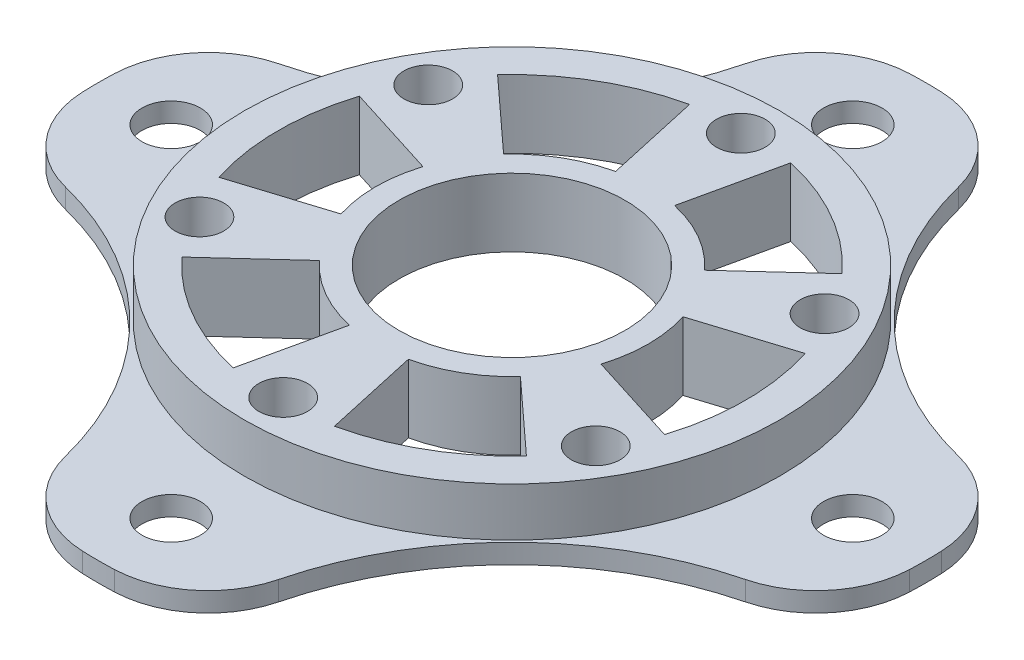
SolidWorks part; units mm, degrees
ref_plane "Front Plane" through (0, 0, 0) normal (0, 0, 1) x (1, 0, 0)
ref_plane "Top Plane" through (0, 0, 0) normal (0, 1, 0) x (1, 0, 0)
ref_plane "Right Plane" through (0, 0, 0) normal (1, 0, 0) x (0, 0, -1)
sketch "Sketch1" plane through (0, 0, 0) normal (0, 1, 0) x (1, 0, 0)
  circle A0 centre (0, 0) radius 27.5
  dimension "D1" = 55
extrude "Boss-Extrude1" add sketch "Sketch1" against normal blind 5
sketch "Sketch2" plane through (0, -5, 0) normal (0, -1, 0) x (1, 0, 0)
  circle A0 centre (0, 0) radius 42.5
  dimension "D1" = 85
extrude "Boss-Extrude2" add sketch "Sketch2" along normal blind 2
sketch "Sketch3" plane through (0, -5, 0) normal (0, 1, 0) x (1, 0, 0)
  circle A0 centre (0, 35) radius 3
  circle A1 centre (35, 0) radius 3
  circle A2 centre (0, -35) radius 3
  circle A3 centre (-35, 0) radius 3
  circle A4 centre (0, 0) radius 42.5 construction
  arc A5 (-10, 41.3068) -> (-41.3068, 10) centre (-42.9586, 42.9586) cw
  arc A6 (41.3068, 10) -> (10, 41.3068) centre (42.9586, 42.9586) cw
  arc A7 (10, -41.3068) -> (41.3068, -10) centre (42.9586, -42.9586) cw
  arc A8 (-41.3068, -10) -> (-10, -41.3068) centre (-42.9586, -42.9586) cw
  circle A10 centre (0, 0) radius 42.5
  circle A11 centre (0, 0) radius 42.5
  point P12 (0, 0)
  point P27 (0, 0)
  circle M3 centre (0, 0) radius 42.5
  dimension "D1" = 6
  dimension "D6" = 33
  dimension "D2" = 35
  dimension "D3" = 4
  dimension "D4" = 10
  dimension "D5" = 10
  dimension "D8" = 0
  dimension "D7" = 4
extrude "Cut-Extrude1" cut sketch "Sketch3" against normal blind 2 contours A5 M3 | A0 | A6 M3 | A1 | A2 | A7 M3 | A8 M3 | A3
sketch "Sketch4" plane through (0, 0, 0) normal (0, 1, 0) x (1, 0, 0)
  circle A0 centre (0, 0) radius 11.6
  circle A1 centre (0, 23.5) radius 2.5
  circle A2 centre (20.3516, 11.75) radius 2.5
  circle A3 centre (20.3516, -11.75) radius 2.5
  circle A4 centre (0, -23.5) radius 2.5
  circle A5 centre (-20.3516, -11.75) radius 2.5
  circle A6 centre (-20.3516, 11.75) radius 2.5
  point P18 (0, 0)
  dimension "D1" = 23.2
  dimension "D2" = 5
  dimension "D3" = 23.5
  dimension "D4" = 6
extrude "Cut-Extrude2" cut sketch "Sketch4" against normal through all
sketch "Sketch5" plane through (0, 0, 0) normal (0, 1, 0) x (1, 0, 0)
  line L0 (-17.6947, 16.2142) -> (-10.3219, 9.4583)
  line L1 (-5.1946, 23.4311) -> (-3.0302, 13.6681)
  line L2 (0, 23.537) -> (0, 0) construction
  line L3 (17.6947, 16.2142) -> (10.3219, 9.4583)
  line L4 (5.1946, 23.4311) -> (3.0302, 13.6681)
  line L5 (22.8892, -7.2169) -> (13.352, -4.2099)
  line L6 (22.8892, 7.2169) -> (13.352, 4.2099)
  line L7 (5.1946, -23.4311) -> (3.0302, -13.6681)
  line L8 (17.6947, -16.2142) -> (10.3219, -9.4583)
  line L9 (-17.6947, -16.2142) -> (-10.3219, -9.4583)
  line L10 (-5.1946, -23.4311) -> (-3.0302, -13.6681)
  line L11 (-22.8892, 7.2169) -> (-13.352, 4.2099)
  line L12 (-22.8892, -7.2169) -> (-13.352, -4.2099)
  arc A0 (-10.3219, 9.4583) -> (-3.0302, 13.6681) centre (0, 0) cw
  arc A1 (-17.6947, 16.2142) -> (-5.1946, 23.4311) centre (0, 0) cw
  arc A2 (5.1946, 23.4311) -> (17.6947, 16.2142) centre (0, 0) cw
  arc A3 (3.0302, 13.6681) -> (10.3219, 9.4583) centre (0, 0) cw
  arc A4 (22.8892, 7.2169) -> (22.8892, -7.2169) centre (0, 0) cw
  arc A5 (13.352, 4.2099) -> (13.352, -4.2099) centre (0, 0) cw
  arc A6 (17.6947, -16.2142) -> (5.1946, -23.4311) centre (0, 0) cw
  arc A7 (10.3219, -9.4583) -> (3.0302, -13.6681) centre (0, 0) cw
  arc A8 (-5.1946, -23.4311) -> (-17.6947, -16.2142) centre (0, 0) cw
  arc A9 (-3.0302, -13.6681) -> (-10.3219, -9.4583) centre (0, 0) cw
  arc A10 (-22.8892, -7.2169) -> (-22.8892, 7.2169) centre (0, 0) cw
  arc A11 (-13.352, -4.2099) -> (-13.352, 4.2099) centre (0, 0) cw
  point P30 (0, 0)
  dimension "D2" = 14
  dimension "D3" = 35
  dimension "D4" = 12.5
  dimension "D1" = 10
  dimension "D5" = 6
extrude "Cut-Extrude3" cut sketch "Sketch5" against normal through all
fillet "Fillet1" radius 10 8 edges at (41.3068, -6, -10) (10, -6, -41.3068) (-10, -6, -41.3068) (-41.3068, -6, -10) (-41.3068, -6, 10) (-10, -6, 41.3068) (10, -6, 41.3068) (41.3068, -6, 10)
